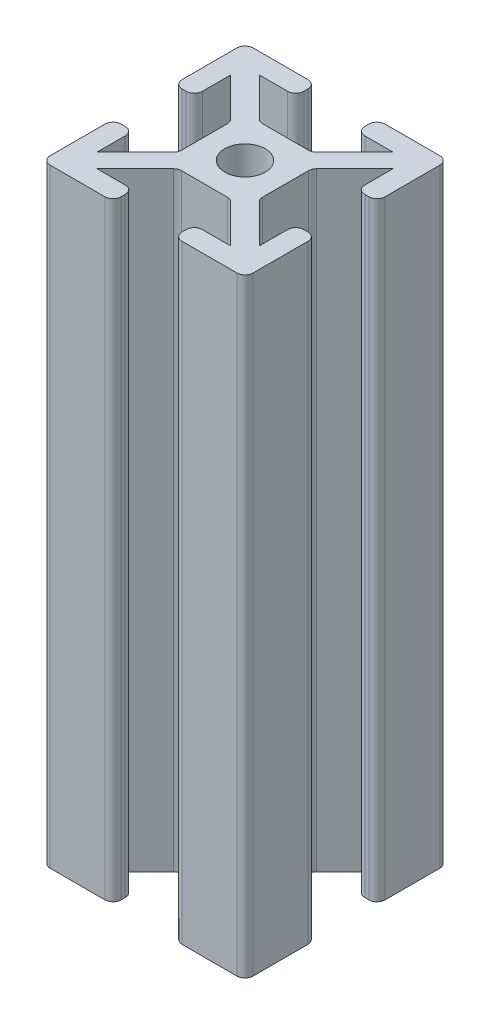
SolidWorks part; units mm, degrees
material "1060 Alloy"
ref_plane "Front Plane" through (0, 0, 0) normal (0, 0, 1) x (1, 0, 0)
ref_plane "Top Plane" through (0, 0, 0) normal (0, 1, 0) x (1, 0, 0)
ref_plane "Right Plane" through (0, 0, 0) normal (1, 0, 0) x (0, 0, -1)
sketch "Sketch2" plane through (0, 0, 0) normal (0, 0, 1) x (1, 0, 0)
  line L0 (0, 34) -> (0, -26)
  dimension "D1" = 60
other "Profile 4X4(1)"
ref_plane "Plane1" through (0, 34, 0) normal (0, -1, 0) x (1, 0, 0)
sketch "Sketch1" plane through (0, 34, 0) normal (0, -1, 0) x (1, 0, 0)
  line L0 (-3, 9.2) -> (-3, 8.8)
  line L1 (-2.2544, 4) -> (2.2544, 4)
  line L2 (-4, 2.2544) -> (-4, -2.2544)
  line L3 (-2.2544, -4) -> (2.2544, -4)
  line L4 (4, 2.2544) -> (4, -2.2544)
  line L7 (-6.5858, 8) -> (-3.8, 8)
  line L8 (-8, 6.5858) -> (-8, 3.8)
  line L9 (-6.5858, -8) -> (-3.8, -8)
  line L10 (8, 6.5858) -> (8, 3.8)
  line L12 (9.7657, -9.7657) -> (10, -10) construction
  line L13 (-9.2, 10) -> (-3.8, 10)
  line L14 (-10, 9.2) -> (-10, 3.8)
  line L15 (-9.2, -10) -> (-3.8, -10)
  line L16 (10, 9.2) -> (10, 3.8)
  line L17 (-10, 10) -> (-9.7657, 9.7657) construction
  line L18 (-10, -10) -> (-9.7657, -9.7657) construction
  line L21 (3, 9.2) -> (3, 8.8)
  line L22 (3, -9.2) -> (3, -8.8)
  line L23 (-3, -9.2) -> (-3, -8.8)
  line L24 (3.8, 10) -> (9.2, 10)
  line L25 (3.8, 8) -> (6.5858, 8)
  line L26 (-9.2, 3) -> (-8.8, 3)
  line L27 (9.2, 3) -> (8.8, 3)
  line L28 (9.2, -3) -> (8.8, -3)
  line L29 (-9.2, -3) -> (-8.8, -3)
  line L30 (-10, -3.8) -> (-10, -9.2)
  line L31 (-8, -3.8) -> (-8, -6.5858)
  line L32 (8, -3.8) -> (8, -6.5858)
  line L33 (10, -3.8) -> (10, -9.2)
  line L34 (3.8, -8) -> (6.5858, -8)
  line L35 (3.8, -10) -> (9.2, -10)
  line L36 (6.5858, 8) -> (2.8201, 4.2343)
  line L37 (8, 6.5858) -> (4.2343, 2.8201)
  line L38 (8, -6.5858) -> (4.2343, -2.8201)
  line L39 (6.5858, -8) -> (2.8201, -4.2343)
  line L40 (-6.5858, -8) -> (-2.8201, -4.2343)
  line L41 (-8, -6.5858) -> (-4.2343, -2.8201)
  line L42 (-8, 6.5858) -> (-4.2343, 2.8201)
  line L43 (-6.5858, 8) -> (-2.8201, 4.2343)
  line L47 (9.7657, 9.7657) -> (10, 10) construction
  circle A0 centre (0, 0) radius 2
  arc A1 (9.2, -3) -> (10, -3.8) centre (9.2, -3.8) cw
  arc A2 (8.8, -3) -> (8, -3.8) centre (8.8, -3.8) ccw
  arc A3 (3, -9.2) -> (3.8, -10) centre (3.8, -9.2) ccw
  arc A4 (3, -8.8) -> (3.8, -8) centre (3.8, -8.8) cw
  arc A5 (-3, -9.2) -> (-3.8, -10) centre (-3.8, -9.2) cw
  arc A6 (-3, -8.8) -> (-3.8, -8) centre (-3.8, -8.8) ccw
  arc A7 (-8.8, -3) -> (-8, -3.8) centre (-8.8, -3.8) cw
  arc A8 (-9.2, -3) -> (-10, -3.8) centre (-9.2, -3.8) ccw
  arc A9 (-10, -9.2) -> (-9.2, -10) centre (-9.2, -9.2) ccw
  arc A10 (9.2, -10) -> (10, -9.2) centre (9.2, -9.2) ccw
  arc A11 (9.2, 10) -> (10, 9.2) centre (9.2, 9.2) cw
  arc A12 (-9.2, 10) -> (-10, 9.2) centre (-9.2, 9.2) ccw
  arc A13 (9.2, 3) -> (10, 3.8) centre (9.2, 3.8) ccw
  arc A14 (8.8, 3) -> (8, 3.8) centre (8.8, 3.8) cw
  arc A15 (3, 9.2) -> (3.8, 10) centre (3.8, 9.2) cw
  arc A16 (3, 8.8) -> (3.8, 8) centre (3.8, 8.8) ccw
  arc A17 (-3, 9.2) -> (-3.8, 10) centre (-3.8, 9.2) ccw
  arc A18 (-3, 8.8) -> (-3.8, 8) centre (-3.8, 8.8) cw
  arc A19 (-8.8, 3) -> (-8, 3.8) centre (-8.8, 3.8) ccw
  arc A20 (-9.2, 3) -> (-10, 3.8) centre (-9.2, 3.8) cw
  arc A21 (-2.8201, 4.2343) -> (-2.2544, 4) centre (-2.2544, 4.8) ccw
  arc A22 (4.2343, 2.8201) -> (4, 2.2544) centre (4.8, 2.2544) ccw
  arc A23 (2.8201, 4.2343) -> (2.2544, 4) centre (2.2544, 4.8) cw
  arc A24 (4.2343, -2.8201) -> (4, -2.2544) centre (4.8, -2.2544) cw
  arc A25 (2.8201, -4.2343) -> (2.2544, -4) centre (2.2544, -4.8) ccw
  arc A26 (-2.8201, -4.2343) -> (-2.2544, -4) centre (-2.2544, -4.8) cw
  arc A27 (-4.2343, -2.8201) -> (-4, -2.2544) centre (-4.8, -2.2544) ccw
  arc A28 (-4.2343, 2.8201) -> (-4, 2.2544) centre (-4.8, 2.2544) cw
  point P7 (0, 0)
  point P10 (-2.5858, 4)
  point P53 (10, -3)
  point P56 (8, -3)
  point P59 (3, -10)
  point P62 (3, -8)
  point P65 (-3, -10)
  point P68 (-3, -8)
  point P71 (-8, -3)
  point P74 (-10, -3)
  point P89 (10, 3)
  point P92 (8, 3)
  point P95 (3, 10)
  point P98 (3, 8)
  point P101 (-3, 10)
  point P104 (-3, 8)
  point P107 (-8, 3)
  point P110 (-10, 3)
  point P116 (4, 2.5858)
  point P119 (2.5858, 4)
  point P122 (4, -2.5858)
  point P125 (2.5858, -4)
  point P128 (-2.5858, -4)
  point P131 (-4, -2.5858)
  point P134 (-4, 2.5858)
  dimension "D3" = 4
  dimension "D11" = 0.8
  dimension "D12" = 0.8
  dimension "D2" = 0.8
  dimension "D4" = 20
  dimension "D6" = 20
  dimension "D8" = 7
  dimension "D9" = 7
